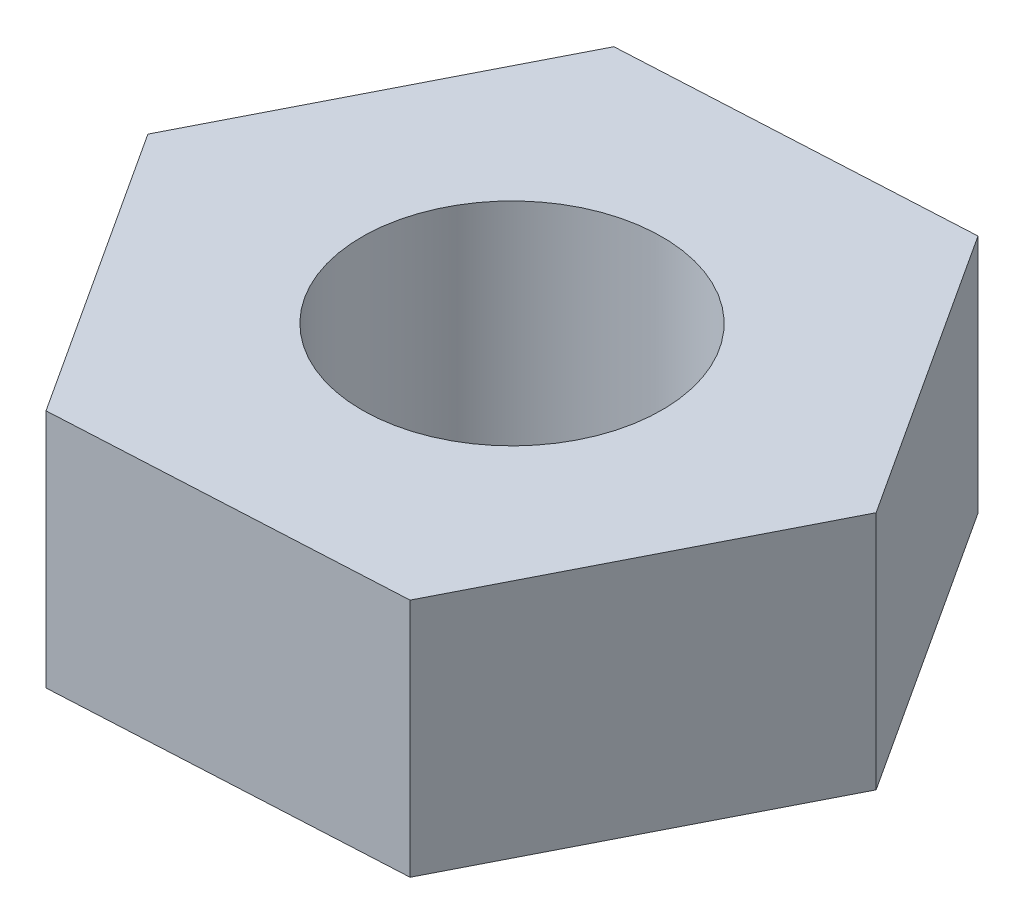
SolidWorks part; units mm, degrees
ref_plane "前视基准面" through (0, 0, 0) normal (0, 0, 1) x (1, 0, 0)
ref_plane "上视基准面" through (0, 0, 0) normal (0, 1, 0) x (1, 0, 0)
ref_plane "右视基准面" through (0, 0, 0) normal (1, 0, 0) x (0, 0, -1)
sketch "草图1" plane through (0, 0, 0) normal (0, 1, 0) x (1, 0, 0)
  line L1 (1.2577, -1.9369) -> (2.3062, 0.1208)
  line L2 (2.3062, 0.1208) -> (1.0485, 2.0576)
  line L3 (1.0485, 2.0576) -> (-1.2577, 1.9369)
  line L4 (-1.2577, 1.9369) -> (-2.3062, -0.1208)
  line L5 (-2.3062, -0.1208) -> (-1.0485, -2.0576)
  line L6 (-1.0485, -2.0576) -> (1.2577, -1.9369)
  circle A0 centre (0, 0) radius 2 construction
  circle A1 centre (0, 0) radius 1
  dimension "D1" = 4
  dimension "D2" = 2
extrude "凸台-拉伸1" add sketch "草图1" along normal blind 1.6
